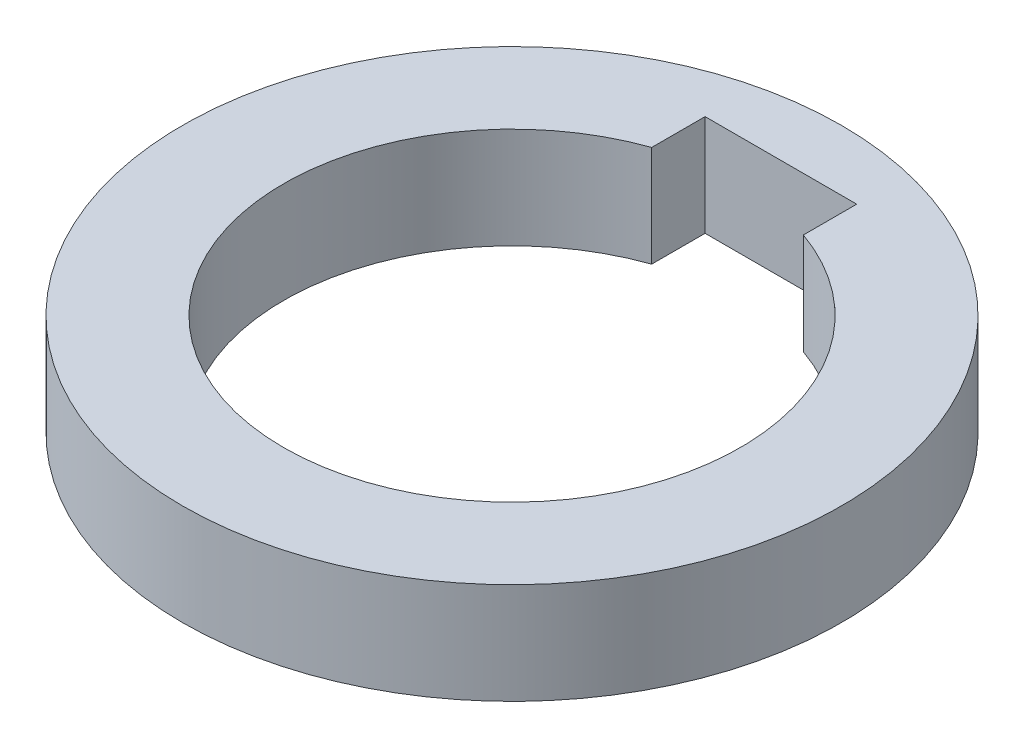
SolidWorks part; units mm, degrees
ref_plane "Alzado" through (0, 0, 0) normal (0, 0, 1) x (1, 0, 0)
ref_plane "Planta" through (0, 0, 0) normal (0, 1, 0) x (1, 0, 0)
ref_plane "Vista lateral" through (0, 0, 0) normal (1, 0, 0) x (0, 0, -1)
sketch "Sketch1" plane through (0, 0, 0) normal (0, 1, 0) x (1, 0, 0)
  line L0 (-7.5, 26.6) -> (-7.5, 21.3192)
  line L1 (7.5, 26.6) -> (7.5, 21.3192)
  line L2 (-7.5, 30.147) -> (-7.5, 24.7982) construction
  line L3 (7.5, 30.147) -> (7.5, 24.7982) construction
  line L4 (-7.5, 26.6) -> (7.5, 26.6)
  circle A0 centre (0, 0) radius 32.6
  arc A1 (-7.5, 21.3192) -> (7.5, 21.3192) centre (0, 0) ccw
  arc A2 (-7.5, 21.3192) -> (7.5, 21.3192) centre (0, 0) cw construction
  point P0 (0, 22.6)
  dimension "D1" = 45.2
  dimension "D2" = 10
  dimension "D4" = 4
  dimension "D3" = 15
extrude "Extrude1" add sketch "Sketch1" along normal blind 10
